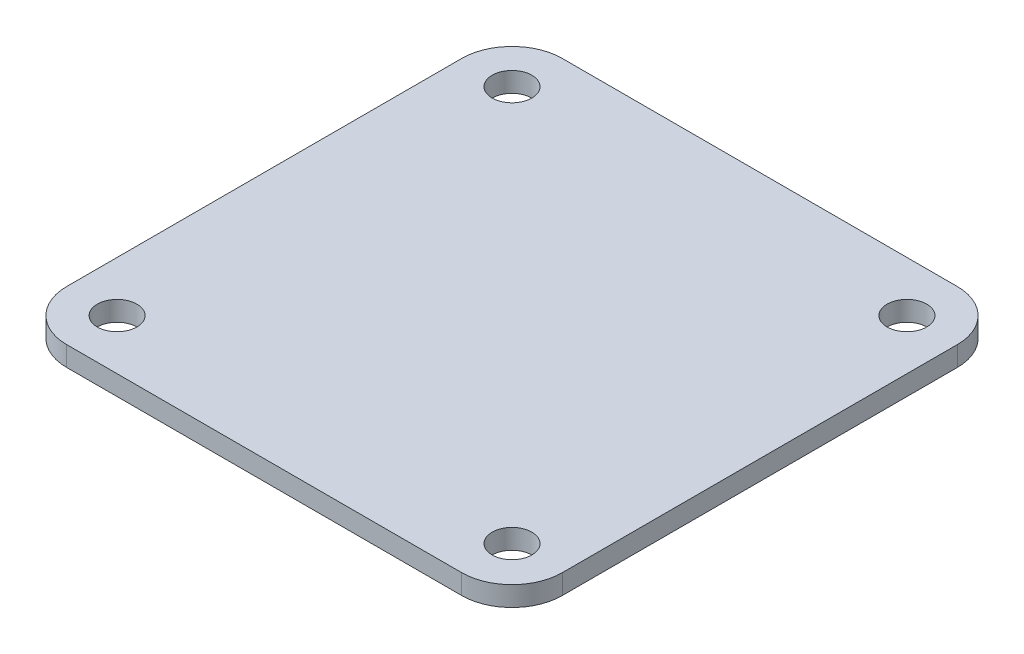
SolidWorks part; units mm, degrees
ref_plane "Front Plane" through (0, 0, 0) normal (0, 0, 1) x (1, 0, 0)
ref_plane "Top Plane" through (0, 0, 0) normal (0, 1, 0) x (1, 0, 0)
ref_plane "Right Plane" through (0, 0, 0) normal (1, 0, 0) x (0, 0, -1)
sketch "Sketch1" plane through (0, 0, 0) normal (0, 1, 0) x (1, 0, 0)
  line L1 (-9.96, -12.5) -> (9.96, -12.5)
  line L2 (-12.5, -9.96) -> (-12.5, 9.96)
  line L3 (-9.96, 12.5) -> (9.96, 12.5)
  line L4 (12.5, -9.96) -> (12.5, 9.96)
  line L5 (-12.5, -12.5) -> (12.5, 12.5) construction
  line L6 (-12.5, 12.5) -> (12.5, -12.5) construction
  line L7 (-10, -10) -> (10, -10) construction
  line L8 (-10, -10) -> (-10, 10) construction
  line L9 (-10, 10) -> (10, 10) construction
  line L10 (10, -10) -> (10, 10) construction
  line L11 (-10, -10) -> (10, 10) construction
  line L12 (-10, 10) -> (10, -10) construction
  arc A0 (-9.96, -12.5) -> (-12.5, -9.96) centre (-9.96, -9.96) cw
  arc A1 (9.96, -12.5) -> (12.5, -9.96) centre (9.96, -9.96) ccw
  arc A2 (9.96, 12.5) -> (12.5, 9.96) centre (9.96, 9.96) cw
  arc A3 (-12.5, 9.96) -> (-9.96, 12.5) centre (-9.96, 9.96) cw
  circle A4 centre (-10, 10) radius 1
  circle A5 centre (9.96, 9.96) radius 1
  circle A6 centre (9.96, -9.96) radius 1
  circle A7 centre (-9.96, -9.96) radius 1
  point P0 (0, 0)
  point P18 (0, 0)
  dimension "D3" = 2.54
  dimension "D6" = 2
  dimension "D7" = 2
  dimension "D8" = 2
  dimension "D9" = 2
  dimension "D1" = 25
  dimension "D2" = 25
  dimension "D4" = 20
  dimension "D5" = 20
extrude "Boss-Extrude1" add sketch "Sketch1" along normal blind 1
